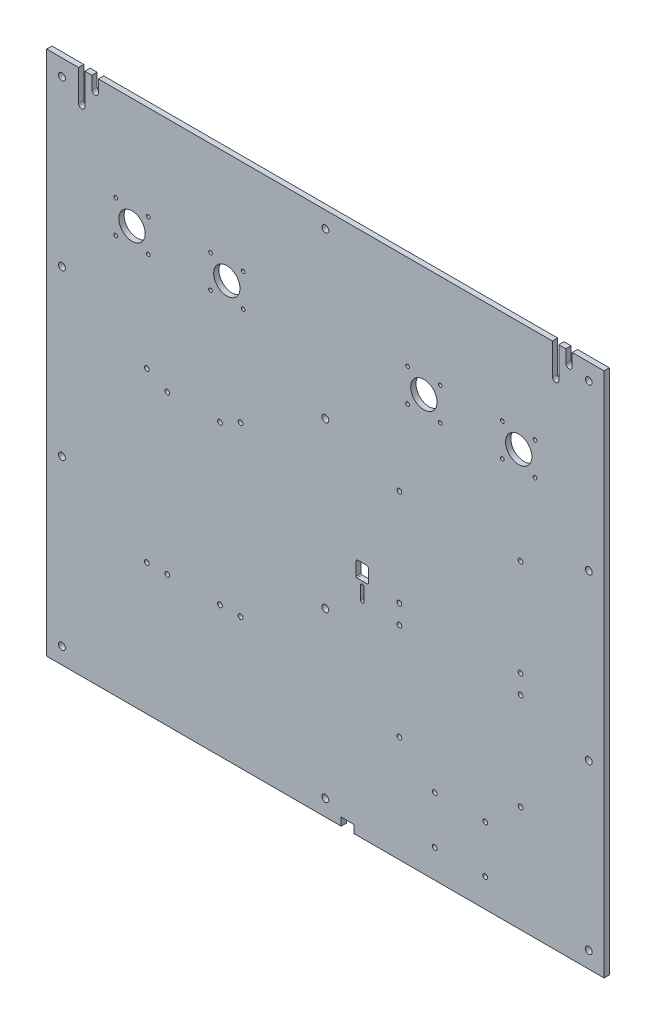
SolidWorks part; units mm, degrees
material "Acrylic (Medium-high impact)"
ref_plane "Front Plane" through (0, 0, 0) normal (0, 0, 1) x (1, 0, 0)
ref_plane "Top Plane" through (0, 0, 0) normal (0, 1, 0) x (1, 0, 0)
ref_plane "Right Plane" through (0, 0, 0) normal (1, 0, 0) x (0, 0, -1)
sketch "Model" plane through (0, 0, 0) normal (0, 0, 1) x (1, 0, 0)
  line L0 (40, -38) -> (30, -38)
  line L1 (29, -37) -> (29, -25)
  line L2 (31, -23) -> (39, -23)
  line L3 (41, -25) -> (41, -37)
  line L4 (-234.25, 220) -> (-234.25, 249.5)
  line L5 (-234.25, 249.5) -> (-264.5, 249.5)
  line L6 (-264.5, 249.5) -> (-264.5, -249.5)
  line L7 (-264.5, -249.5) -> (15, -249.5)
  line L8 (15, -249.5) -> (15, -242)
  line L9 (15, -242) -> (27, -242)
  line L10 (27, -242) -> (27, -249.5)
  line L11 (27, -249.5) -> (264.5, -249.5)
  line L12 (264.5, -249.5) -> (264.5, 249.5)
  line L13 (264.5, 249.5) -> (234.25, 249.5)
  line L14 (234.25, 249.5) -> (234.25, 237.5)
  line L15 (228.25, 237.5) -> (228.25, 249.5)
  line L16 (228.25, 249.5) -> (221.5, 249.5)
  line L17 (221.5, 249.5) -> (221.5, 220)
  line L18 (215.5, 220) -> (215.5, 249.5)
  line L19 (215.5, 249.5) -> (-215.5, 249.5)
  line L20 (-215.5, 249.5) -> (-215.5, 237.5)
  line L21 (-221.5, 237.5) -> (-221.5, 249.5)
  line L22 (-221.5, 249.5) -> (-228.25, 249.5)
  line L23 (-228.25, 249.5) -> (-228.25, 220)
  line L24 (36.6, -42) -> (36.6, -54.5)
  line L25 (33.4, -54.5) -> (33.4, -42)
  circle A0 centre (0, 234) radius 3.25
  circle A1 centre (250, 78) radius 3.25
  circle A2 centre (250, -234) radius 3.25
  circle A3 centre (250, -78) radius 3.25
  circle A4 centre (151.75, -177.5) radius 2.25
  circle A5 centre (0, -234) radius 3.25
  circle A6 centre (0, -78) radius 3.25
  circle A7 centre (0, 78) radius 3.25
  circle A8 centre (70.25, -38.5) radius 2.25
  circle A9 centre (185.25, -56.5) radius 2.25
  circle A10 centre (185.25, -148.5) radius 2.25
  circle A11 centre (70.25, -148.5) radius 2.25
  circle A12 centre (70.25, -56.5) radius 2.25
  circle A13 centre (70.25, 53.5) radius 2.25
  circle A14 centre (185.25, 53.5) radius 2.25
  circle A15 centre (185.25, -38.5) radius 2.25
  circle A16 centre (199, 160) radius 1.75
  circle A17 centre (199, 129) radius 1.75
  circle A18 centre (168, 129) radius 1.75
  circle A19 centre (168, 160) radius 1.75
  circle A20 centre (109, 160) radius 1.75
  circle A21 centre (78, 129) radius 1.75
  circle A22 centre (78, 160) radius 1.75
  circle A23 centre (109, 129) radius 1.75
  circle A24 centre (-109, 129) radius 1.75
  circle A25 centre (-109, 160) radius 1.75
  circle A26 centre (-78, 129) radius 1.75
  circle A27 centre (-78, 160) radius 1.75
  circle A28 centre (-199, 129) radius 1.75
  circle A29 centre (-168, 129) radius 1.75
  circle A30 centre (-168, 160) radius 1.75
  circle A31 centre (-199, 160) radius 1.75
  circle A32 centre (-250, 78) radius 3.25
  circle A33 centre (-250, -78) radius 3.25
  circle A34 centre (-250, -234) radius 3.25
  circle A35 centre (-250, 234) radius 3.25
  circle A36 centre (-100, -125) radius 2.25
  circle A37 centre (-100, 25) radius 2.25
  circle A38 centre (-150, 25) radius 2.25
  circle A39 centre (250, 234) radius 3.25
  circle A40 centre (-150, -125) radius 2.25
  circle A41 centre (103.75, -177.5) radius 2.25
  circle A42 centre (-183.5, 144.5) radius 12.5
  circle A45 centre (-93.5, 144.5) radius 12.5
  circle A46 centre (93.5, 144.5) radius 12.5
  circle A49 centre (183.5, 144.5) radius 12.5
  circle A50 centre (-169.5, -125) radius 2.25
  circle A51 centre (-80.5, 34.5) radius 2.25
  circle A52 centre (-169.5, 34.5) radius 2.25
  circle A53 centre (-80.5, -125) radius 2.25
  circle A54 centre (151.75, -222.4991) radius 2.25
  circle A55 centre (103.75, -222.4991) radius 2.25
  arc A56 (40, -38) -> (41, -37) centre (40, -37) ccw
  arc A57 (29, -37) -> (30, -38) centre (30, -37) ccw
  arc A58 (31, -23) -> (29, -25) centre (31, -25) ccw
  arc A59 (41, -25) -> (39, -23) centre (39, -25) ccw
  arc A60 (-234.25, 220) -> (-228.25, 220) centre (-231.25, 220) ccw
  arc A61 (228.25, 237.5) -> (234.25, 237.5) centre (231.25, 237.5) ccw
  arc A62 (215.5, 220) -> (221.5, 220) centre (218.5, 220) ccw
  arc A63 (-221.5, 237.5) -> (-215.5, 237.5) centre (-218.5, 237.5) ccw
  arc A64 (36.6, -42) -> (33.4, -42) centre (35, -42) ccw
  arc A65 (33.4, -54.5) -> (36.6, -54.5) centre (35, -54.5) ccw
  dimension "D1" = 6.5
  dimension "D2" = 3.5
  dimension "D3" = 4.5
  dimension "D4" = 12.5
  dimension "D5" = 1
  dimension "D6" = 2
  dimension "D7" = 3
  dimension "D8" = 1.6
  dimension "D28" = 25
  dimension "D47" = 25
  dimension "D51" = 183.5
  dimension "D52" = 218.5
  dimension "D53" = 264.5
  dimension "D54" = 23
  dimension "D9" = 15
  dimension "D10" = 27
  dimension "D11" = 35
  dimension "D12" = 41
  dimension "D13" = 70.25
  dimension "D14" = 78
  dimension "D15" = 93.5
  dimension "D16" = 103.75
  dimension "D17" = 109
  dimension "D18" = 151.75
  dimension "D19" = 168
  dimension "D20" = 12
  dimension "D21" = 185.25
  dimension "D22" = 199
  dimension "D23" = 250
  dimension "D24" = 78
  dimension "D25" = 80.5
  dimension "D26" = 15
  dimension "D27" = 93.5
  dimension "D29" = 100
  dimension "D30" = 109
  dimension "D31" = 150
  dimension "D32" = 168
  dimension "D33" = 169.5
  dimension "D34" = 183.5
  dimension "D35" = 199
  dimension "D36" = 218.5
  dimension "D37" = 231.25
  dimension "D38" = 250
  dimension "D39" = 264.5
  dimension "D40" = 25
  dimension "D41" = 34.5
  dimension "D42" = 53.5
  dimension "D43" = 78
  dimension "D44" = 129
  dimension "D45" = 237.5
  dimension "D46" = 242
  dimension "D48" = 160
  dimension "D49" = 220
  dimension "D50" = 234
  dimension "D55" = 38.5
  dimension "D56" = 42
  dimension "D57" = 54.5
  dimension "D58" = 56.5
  dimension "D59" = 78
  dimension "D60" = 125
  dimension "D61" = 148.5
  dimension "D62" = 177.5
  dimension "D63" = 222.4991
  dimension "D64" = 234
  dimension "D66" = 249.5
  dimension "D70" = 144.5
extrude "Boss-Extrude1" add sketch "Model" along normal blind 5
